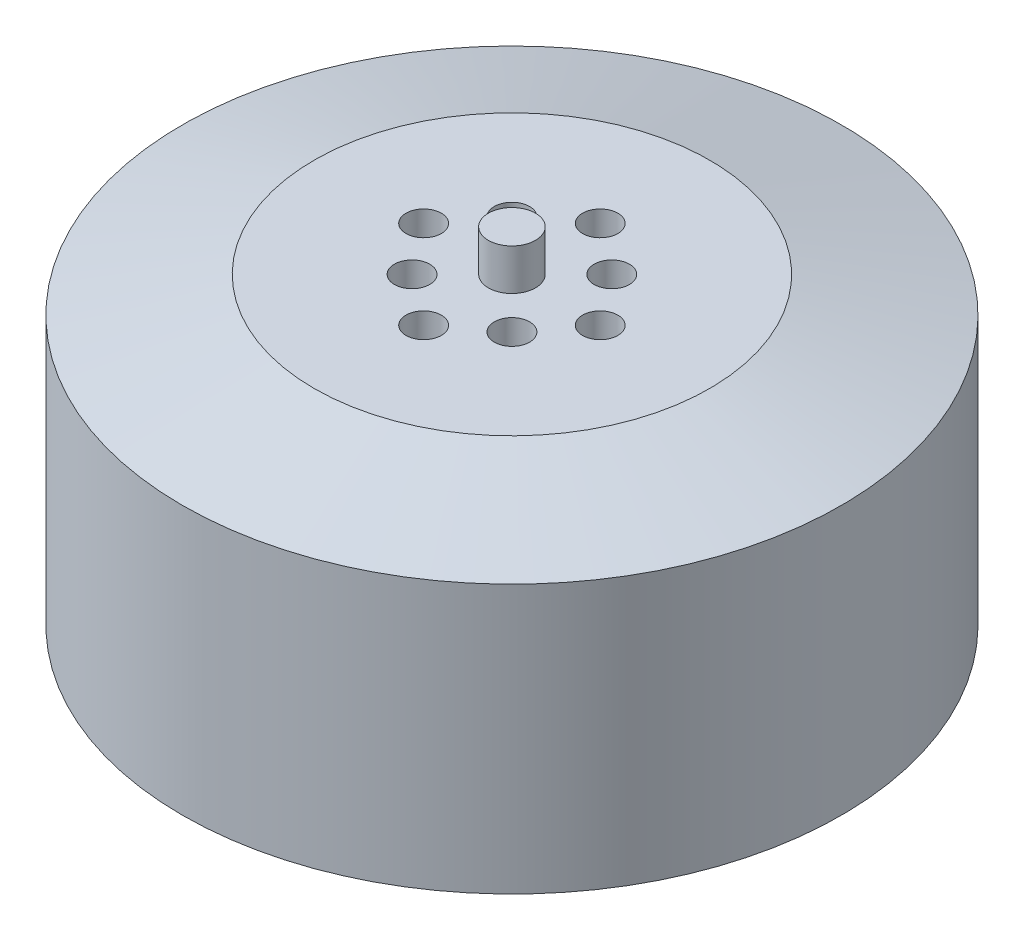
SolidWorks part; units mm, degrees
ref_plane "Front Plane" through (0, 0, 0) normal (0, 0, 1) x (1, 0, 0)
ref_plane "Top Plane" through (0, 0, 0) normal (0, 1, 0) x (1, 0, 0)
ref_plane "Right Plane" through (0, 0, 0) normal (1, 0, 0) x (0, 0, -1)
sketch "Sketch1" plane through (0, 0, 0) normal (0, 1, 0) x (1, 0, 0)
  circle A0 centre (0, 0) radius 28
  dimension "D1" = 56
extrude "Boss-Extrude1" add sketch "Sketch1" along normal blind 25.8
sketch "Sketch2" plane through (0, 25.8, 0) normal (0, 1, 0) x (1, 0, 0)
  circle A0 centre (0, 0) radius 2
  dimension "D1" = 4
extrude "Boss-Extrude2" add sketch "Sketch2" along normal blind 3.5
sketch "Sketch3" plane through (0, 0, 0) normal (0, -1, 0) x (1, 0, 0)
  circle A0 centre (0, 0) radius 15 construction
  circle A1 centre (0, 15) radius 1.5
  circle A2 centre (15, 0) radius 1.5
  circle A3 centre (0, -15) radius 1.5
  circle A4 centre (-15, 0) radius 1.5
  point P14 (0, 0)
  dimension "D1" = 30
  dimension "D2" = 3
  dimension "D3" = 4
extrude "Cut-Extrude1" cut sketch "Sketch3" against normal blind 3
sketch "Sketch4" plane through (0, 25.8, 0) normal (0, 1, 0) x (1, 0, 0)
  line L0 (0, 0) -> (5.3033, 5.3033) construction
  line L1 (0, 0) -> (7.5, 0) construction
  circle A0 centre (0, 0) radius 7.5 construction
  circle A1 centre (0, 0) radius 6 construction
  circle A2 centre (0, 7.5) radius 1.5
  circle A3 centre (7.5, 0) radius 1.5
  circle A4 centre (0, -7.5) radius 1.5
  circle A5 centre (-7.5, 0) radius 1.5
  circle A6 centre (4.2426, 4.2426) radius 1.5
  circle A7 centre (4.2426, -4.2426) radius 1.5
  circle A8 centre (-4.2426, -4.2426) radius 1.5
  circle A9 centre (-4.2426, 4.2426) radius 1.5
  point P15 (0, 0)
  point P25 (0, 0)
  dimension "D1" = 15
  dimension "D2" = 12
  dimension "D3" = 3
  dimension "D6" = 3
  dimension "D5" = 45
  dimension "D4" = 4
  dimension "D7" = 4
extrude "Cut-Extrude2" cut sketch "Sketch4" against normal blind 3
chamfer "Chamfer1" distance 3 angle 75 1 edges at (0, 25.8, 28)
